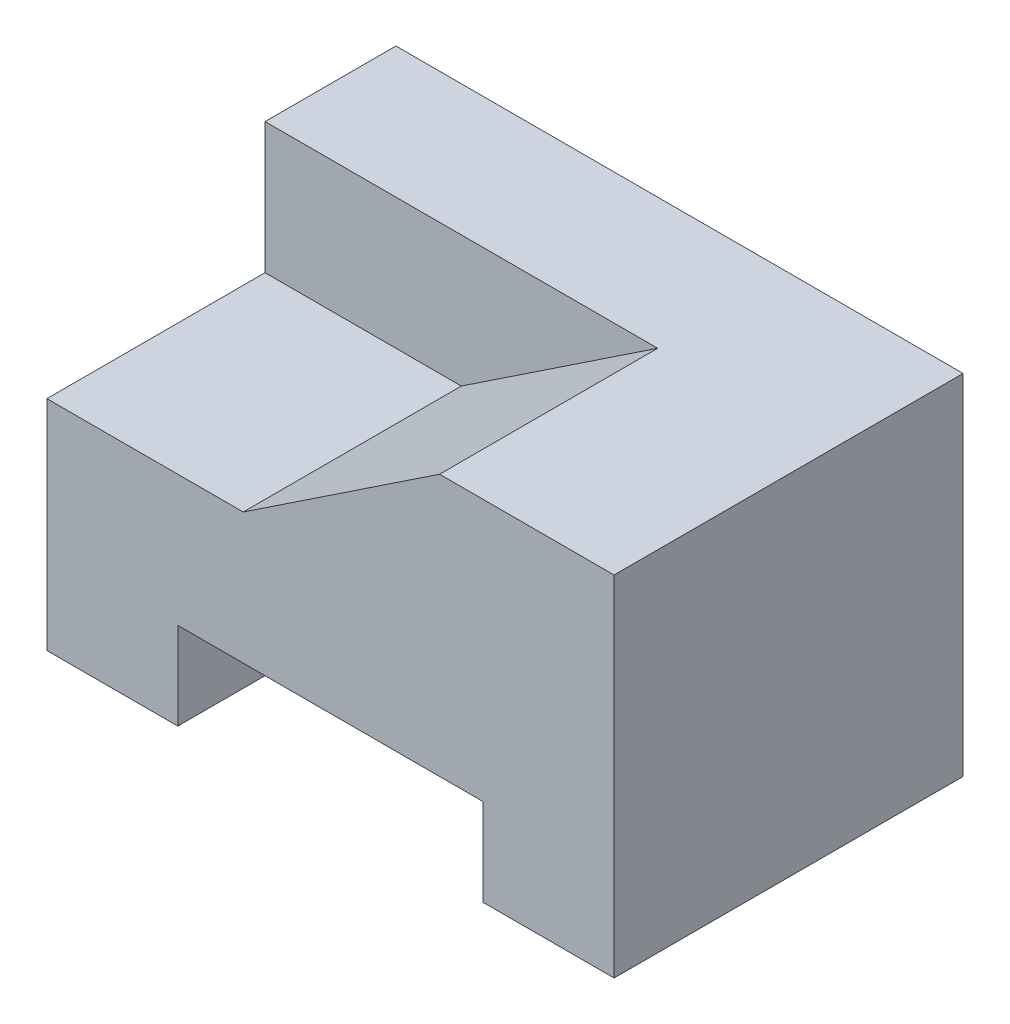
SolidWorks part; units mm, degrees
ref_plane "Front" through (0, 0, 0) normal (0, 0, 1) x (1, 0, 0)
ref_plane "Top" through (0, 0, 0) normal (0, 1, 0) x (1, 0, 0)
ref_plane "Right" through (0, 0, 0) normal (1, 0, 0) x (0, 0, -1)
sketch "Sketch1" plane through (0, 0, 0) normal (0, 0, 1) x (1, 0, 0)
  line L1 (0, 0) -> (13, 0)
  line L2 (0, 0) -> (0, 8)
  line L3 (0, 8) -> (13, 8)
  line L4 (13, 0) -> (13, 8)
  line L5 (3, 0) -> (10, 0)
  line L6 (3, 0) -> (3, 2)
  line L7 (3, 2) -> (10, 2)
  line L8 (10, 0) -> (10, 2)
  dimension "D1" = 13
  dimension "D2" = 8
  dimension "D3" = 2
  dimension "D4" = 3
  dimension "D5" = 3
extrude "Boss-Extrude1" add sketch "Sketch1" along normal blind 8 contours L8 L1 L4 L3 L2 L6 L7
sketch "Sketch2" plane through (0, 0, 8) normal (0, 0, 1) x (1, 0, 0)
  line L0 (9, 8) -> (4.5, 5)
  line L1 (0, 8) -> (13, 8) construction
  line L2 (4.5, 5) -> (0, 5)
  line L3 (0, 0) -> (0, 8) construction
  line L4 (0, 5) -> (0, 8)
  line L5 (0, 8) -> (9, 8)
  dimension "D1" = 3
  dimension "D2" = 9
  dimension "D3" = 4.5
extrude "Cut-Extrude1" cut sketch "Sketch2" against normal blind 5
